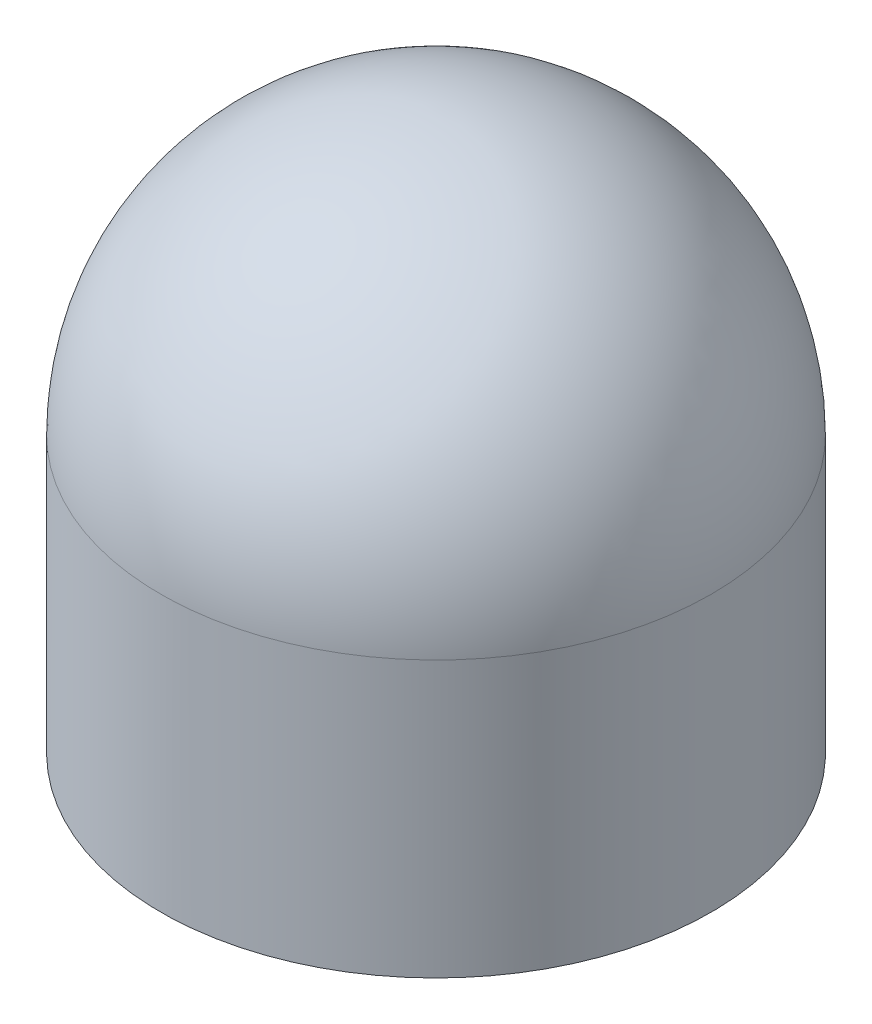
SolidWorks part; units mm, degrees
material "Polyester Resin"
ref_plane "Front Plane" through (0, 0, 0) normal (0, 0, 1) x (1, 0, 0)
ref_plane "Top Plane" through (0, 0, 0) normal (0, 1, 0) x (1, 0, 0)
ref_plane "Right Plane" through (0, 0, 0) normal (1, 0, 0) x (0, 0, -1)
sketch "Sketch1" plane through (0, 0, 0) normal (0, 0, 1) x (1, 0, 0)
  line L0 (0, 0) -> (30, 0)
  line L3 (0, 0) -> (0, 60)
  line L4 (0, 30) -> (30, 30) construction
  line L25 (30, 30) -> (30, 0) construction
  line L29 (30, 30) -> (30, 0)
  arc A0 (30, 30) -> (0, 60) centre (0, 30) ccw
  dimension "D1" = 30
  dimension "D2" = 30
revolve "Revolve1" add sketch "Sketch1" angle 360 about L3
equation "\"d\"= 60mm"
equation "\"h\"= \"d\" / 2"
equation "\"D1@Sketch1\"=\"d\"/2"
equation "\"D2@Sketch1\"=\"h\""
